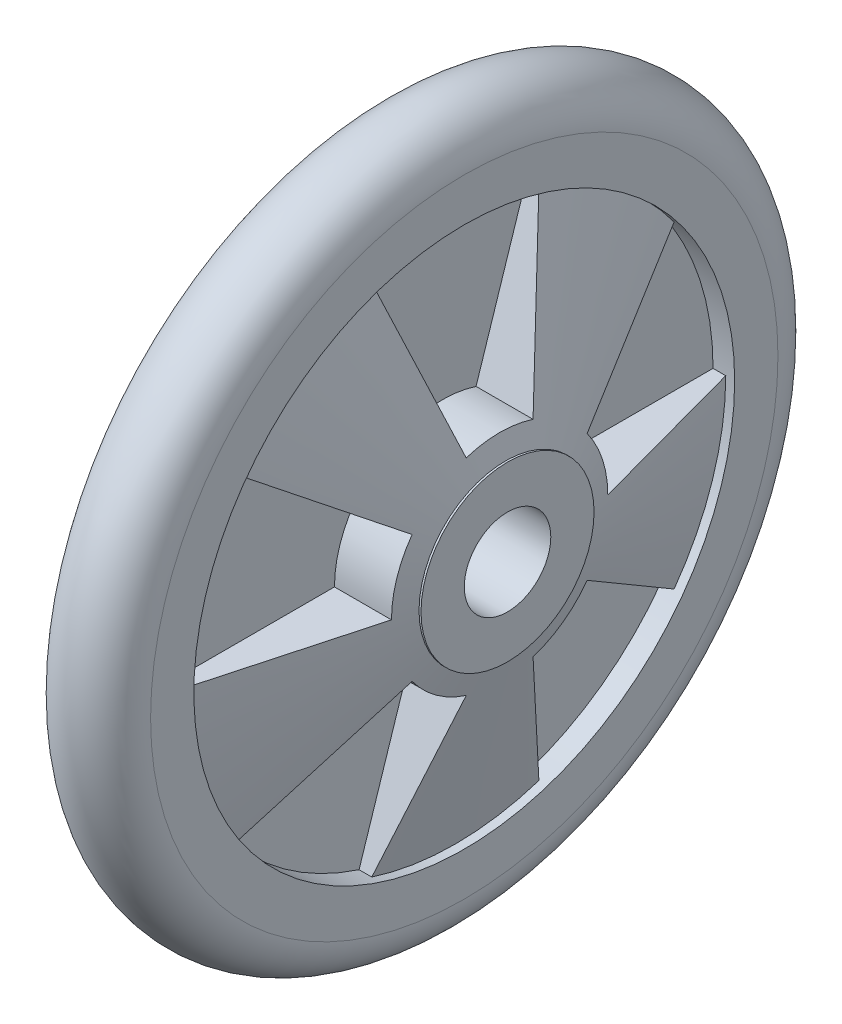
SolidWorks part; units mm, degrees
ref_plane "Front Plane" through (0, 0, 0) normal (0, 0, 1) x (1, 0, 0)
ref_plane "Top Plane" through (0, 0, 0) normal (0, 1, 0) x (1, 0, 0)
ref_plane "Right Plane" through (0, 0, 0) normal (1, 0, 0) x (0, 0, -1)
sketch "Sketch1" plane through (0, 0, 0) normal (1, 0, 0) x (0, 0, -1)
  circle A0 centre (0, 0) radius 72.5
  dimension "D1" = 145
sketch "Sketch3" plane through (0, 0, 0) normal (0, 0, 1) x (1, 0, 0)
  line L0 (0, 0) -> (0, 72.5) construction
  line L1 (0, -79.75) -> (0, 79.75) construction
  line L2 (10, 72.5) -> (10, 62.5)
  line L3 (10, 62.5) -> (-10, 62.5)
  line L4 (-10, 62.5) -> (-10, 72.5)
  arc A0 (10, 72.5) -> (-10, 72.5) centre (0, 72.5) ccw
  dimension "D2" = 20
  dimension "D1" = 72.5
sweep "Sweep1" add profiles "Sketch3" path "Sketch1"
sketch "Sketch4" plane through (0, 0, 0) normal (1, 0, 0) x (0, 0, -1)
  line L0 (0, 0) -> (0, 88.7463) construction
  line L1 (25, 0) -> (62.5, 0)
  line L2 (7.7254, 23.7764) -> (19.3136, 59.441)
  line L3 (-7.7254, 23.7764) -> (-19.3136, 59.441)
  line L4 (20.2254, 14.6946) -> (50.5636, 36.7366)
  line L5 (0, 0) -> (84.4027, 27.4241) construction
  line L6 (7.7254, -23.7764) -> (19.3136, -59.441)
  line L7 (20.2254, -14.6946) -> (50.5636, -36.7366)
  line L8 (0, 0) -> (52.1637, -71.7972) construction
  line L9 (-20.2254, -14.6946) -> (-50.5636, -36.7366)
  line L10 (-7.7254, -23.7764) -> (-19.3136, -59.441)
  line L11 (0, 0) -> (-52.1637, -71.7972) construction
  line L12 (-20.2254, 14.6946) -> (-50.5636, 36.7366)
  line L13 (-25, 0) -> (-62.5, 0)
  line L14 (0, 0) -> (-84.4027, 27.4241) construction
  circle A0 centre (0, 0) radius 72.5
  arc A1 (7.7254, -23.7764) -> (20.2254, -14.6946) centre (0, 0) ccw
  circle A2 centre (0, 0) radius 62.5 construction
  arc A3 (19.3136, -59.441) -> (50.5636, -36.7366) centre (0, 0) ccw
  arc A4 (25, 0) -> (20.2254, 14.6946) centre (0, 0) ccw
  arc A5 (62.5, 0) -> (50.5636, 36.7366) centre (0, 0) ccw
  arc A6 (7.7254, 23.7764) -> (-7.7254, 23.7764) centre (0, 0) ccw
  arc A7 (19.3136, 59.441) -> (-19.3136, 59.441) centre (0, 0) ccw
  arc A8 (-20.2254, 14.6946) -> (-25, 0) centre (0, 0) ccw
  arc A9 (-50.5636, 36.7366) -> (-62.5, 0) centre (0, 0) ccw
  arc A10 (-20.2254, -14.6946) -> (-7.7254, -23.7764) centre (0, 0) ccw
  arc A11 (-50.5636, -36.7366) -> (-19.3136, -59.441) centre (0, 0) ccw
  point P33 (0, 0)
  dimension "D1" = 145
  dimension "D2" = 50
  dimension "D3" = 18
  dimension "D4" = 5
extrude "Boss-Extrude7" add sketch "Sketch4" along normal mid plane 50 separate body
sketch "Sketch12" plane through (0, 0, 0) normal (0, 0, 1) x (1, 0, 0)
  line L0 (-25, 0) -> (-32.1406, 0)
  line L3 (-25, 72.5) -> (-25, -72.5) construction
  line L4 (0, 92.1309) -> (0, -15.608) construction
  line L5 (0, -171.4222) -> (0, 171.4222) construction
  line L6 (-5.0166, 92.1293) -> (-5.0166, 66.8334) construction
  line L7 (-10.0332, 92.1293) -> (0, 92.1293) construction
  line L8 (-46.8402, 0) -> (93.6803, 0) construction
  line L9 (25, 0) -> (-25, 0) construction
  line L10 (-32.1406, 0) -> (-32.1406, 73.1916)
  line L11 (-32.1406, 73.1916) -> (-5.0166, 73.1916)
  line L12 (-5.0166, 73.1916) -> (-25, 0)
  line L13 (25, 0) -> (32.1406, 0)
  line L14 (32.1406, 0) -> (32.1406, 73.1916)
  line L15 (32.1406, 73.1916) -> (5.0166, 73.1916)
  line L16 (5.0166, 73.1916) -> (25, 0)
revolve "Cut-Revolve11" cut sketch "Sketch12" angle 360
sketch "Sketch13" plane through (0, 0, 0) normal (1, 0, 0) x (0, 0, -1)
  circle A0 centre (0, 0) radius 72.5
extrude "Boss-Extrude8" add sketch "Sketch13" along normal mid plane 10
sketch "Sketch14" plane through (0, 0, 0) normal (1, 0, 0) x (0, 0, -1)
  circle A1 centre (0, 0) radius 20
  dimension "D1" = 40
extrude "Cut-Extrude1" cut sketch "Sketch14" against normal mid plane 50
sketch "Sketch15" plane through (0, 0, 0) normal (1, 0, 0) x (0, 0, -1)
  circle A0 centre (0, 0) radius 10
  circle A1 centre (0, 0) radius 20
  dimension "D1" = 20
extrude "Boss-Extrude10" add sketch "Sketch15" along normal mid plane 40
equation "\"ๅถ\"=50"
